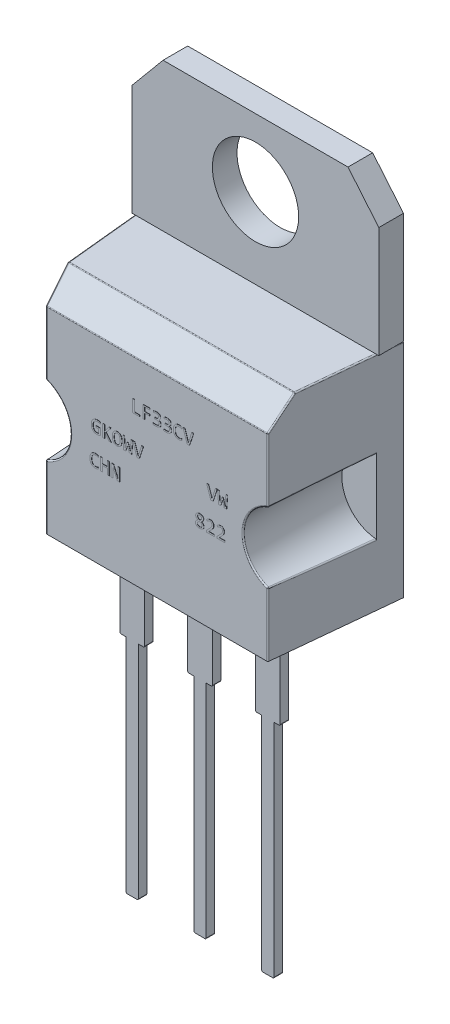
SolidWorks part; units mm, degrees
ref_plane "Alzado" through (0, 0, 0) normal (0, 0, 1) x (1, 0, 0)
ref_plane "Planta" through (0, 0, 0) normal (0, 1, 0) x (1, 0, 0)
ref_plane "Vista lateral" through (0, 0, 0) normal (1, 0, 0) x (0, 0, -1)
sketch "Croquis1" plane through (0, 0, 0) normal (0, 1, 0) x (1, 0, 0)
  line L0 (-5, 2.5) -> (5, -2.5) construction
  line L1 (-5, 2.5) -> (5, 2.5)
  line L2 (-5, 2.5) -> (-5, -2.5)
  line L3 (-5, -2.5) -> (5, -2.5)
  line L4 (5, 2.5) -> (5, -2.5)
  dimension "D1" = 5
  dimension "D2" = 10
extrude "Extruir1" add sketch "Croquis1" along normal blind 9
sketch "Croquis2" plane through (0, 0, 2.5) normal (0, 0, 1) x (1, 0, 0)
  line L0 (5, 0) -> (5, 2.5) construction
  line L1 (5, 9) -> (5, 0) construction
  line L2 (5, 2.5) -> (5, 4) construction
  line L3 (0, 0) -> (0, 2.735) construction
  line L4 (-5, 2.5) -> (-5, 4) construction
  line L5 (-5, 0) -> (-5, 2.5) construction
  line L6 (-5, 5.5) -> (-5, 2.5)
  line L7 (5, 2.5) -> (5, 5.5)
  arc A0 (5, 2.5) -> (5, 5.5) centre (5, 4) cw
  arc A1 (-5, 2.5) -> (-5, 5.5) centre (-5, 4) ccw
  dimension "D1" = 2.5
  dimension "D2" = 1.5
extrude "Extruir2" cut sketch "Croquis2" against normal blind 4
chamfer "Chaflán1" distance 1 angle 45 1 edges at (0, 9, 2.5)
fillet "Redondeo1" radius 0.05 2 edges at (0, 9, 1.5) (0, 8, 2.5)
sketch "Croquis3" plane through (0, 9, 0) normal (0, 1, 0) x (1, 0, 0)
  line L0 (5, -1.4793) -> (5, 2.5) construction
  line L1 (-5, 2.5) -> (5, 2.5)
  line L2 (-5, 2.5) -> (-5, 1.5)
  line L3 (-5, 1.5) -> (5, 1.5)
  line L4 (5, 2.5) -> (5, 1.5)
  dimension "D1" = 1
extrude "Extruir3" add sketch "Croquis3" along normal blind 6 separate body
sketch "Croquis4" plane through (0, 0, -1.5) normal (0, 0, 1) x (1, 0, 0)
  line L0 (-5, 15) -> (-3.75, 15)
  line L1 (-5, 15) -> (5, 15) construction
  line L2 (-5, 15) -> (-5, 9) construction
  line L3 (-5, 15) -> (-5, 13.5)
  line L4 (-5, 13.5) -> (-3.75, 15)
  line L5 (0, 0) -> (0, 3.6295) construction
  line L6 (5, 13.5) -> (3.75, 15)
  line L7 (5, 15) -> (5, 13.5)
  line L8 (5, 15) -> (3.75, 15)
  line L9 (0, 15) -> (0, 14) construction
  circle A0 centre (0, 12.25) radius 1.75
  dimension "D4" = 3.5
  dimension "D1" = 1.25
  dimension "D2" = 1.5
  dimension "D3" = 1
extrude "Extruir4" cut sketch "Croquis4" against normal through all
sketch "Croquis5" plane through (0, 0, 0) normal (0, -1, 0) x (1, 0, 0)
  line L0 (5, 1) -> (5, 2.5) construction
  line L2 (3.5, 2.5) -> (5, 2.5) construction
  line L3 (-5, 2.5) -> (5, 2.5) construction
  line L4 (5, 2.5) -> (5, -2.5) construction
  line L5 (3.5, 1) -> (3.5, 2.5) construction
  line L6 (3.5, 1) -> (2.5, 1)
  line L7 (3.5, 1) -> (3.5, 0.66)
  line L8 (3.5, 0.66) -> (2.5, 0.66)
  line L9 (2.5, 1) -> (2.5, 0.66)
  dimension "D1" = 1.5
  dimension "D2" = 1.5
  dimension "D3" = 1
  dimension "D4" = 0.34
extrude "Extruir5" add sketch "Croquis5" along normal blind 3.5
sketch "Croquis6" plane through (0, -3.5, 0) normal (0, -1, 0) x (1, 0, 0)
  line L0 (3.5, 0.83) -> (3.25, 0.83) construction
  line L1 (3.5, 0.66) -> (3.5, 1) construction
  line L2 (2.5, 0.66) -> (3.5, 0.66) construction
  line L3 (3.25, 1) -> (2.75, 1)
  line L4 (3.25, 1) -> (3.25, 0.66)
  line L5 (3.25, 0.66) -> (2.75, 0.66)
  line L6 (2.75, 1) -> (2.75, 0.66)
  line L7 (3.25, 1) -> (2.75, 0.66) construction
  line L8 (3.25, 0.66) -> (2.75, 1) construction
  point P4 (3, 0.83)
  dimension "D1" = 0.25
  dimension "D2" = 0.5
extrude "Extruir6" add sketch "Croquis6" along normal blind 9
fillet "Redondeo2" radius 0.05 4 edges at (3.25, -12.5, 0.83) (3.5, -3.5, 0.83) (2.75, -12.5, 0.83) (2.5, -3.5, 0.83)
pattern_linear "MatrizL1" count 3 spacing 2.75 along (-1, 0, 0) of "Extruir5", "Extruir6", "Redondeo2"
sketch "Croquis7" plane through (0, 0, 0) normal (0, -1, 0) x (1, 0, 0)
  line L0 (5, -2.5) -> (5, 2.5)
  line L1 (5, 2.5) -> (4.5, 2.5)
  line L2 (-5, 2.5) -> (5, 2.5) construction
  line L3 (5, -2.5) -> (4.5, 2.5)
  line L4 (0, -2.5) -> (0, -1.1989) construction
  line L5 (5, -2.5) -> (-5, -2.5) construction
  line L6 (-5, -2.5) -> (-4.5, 2.5)
  line L7 (-5, 2.5) -> (-4.5, 2.5)
  line L8 (-5, -2.5) -> (-5, 2.5)
  dimension "D1" = 0.5
extrude "Extruir7" cut sketch "Croquis7" against normal blind 9
fillet "Redondeo3" radius 0.05 18 edges at (-4.801, 9, -0.5104) (-4.6002, 8.9962, 1.4984) (-4.55, 8.5, 2) (-4.5004, 7.9984, 2.4962) (4.801, 9, -0.5104) (4.6002, 8.9962, 1.4984) (4.5004, 7.9984, 2.4962) (4.55, 8.5, 2) (-4.5, 6.6968, 2.5) (-3.5, 4, 2.5) (-4.5, 1.2929, 2.5) (4.5, 1.2929, 2.5) (3.5, 4, 2.5) (4.5, 6.6968, 2.5) (-4.6972, 5.4691, 0.5282) (-4.6972, 2.5309, 0.5282) (4.6972, 2.5309, 0.5282) (4.6972, 5.4691, 0.5282)
sketch "Croquis8" plane through (0, 0, 2.5) normal (0, 0, 1) x (1, 0, 0)
  text T0 "LF33CV" font "Consolas" height 0.5
  text T1 " GKOWV      VW" font "Consolas" height 0.5
  text T2 "CHN       822" font "Consolas" height 0.5
extrude "Extruir8" add sketch "Croquis8" along normal blind 0.01 separate body
